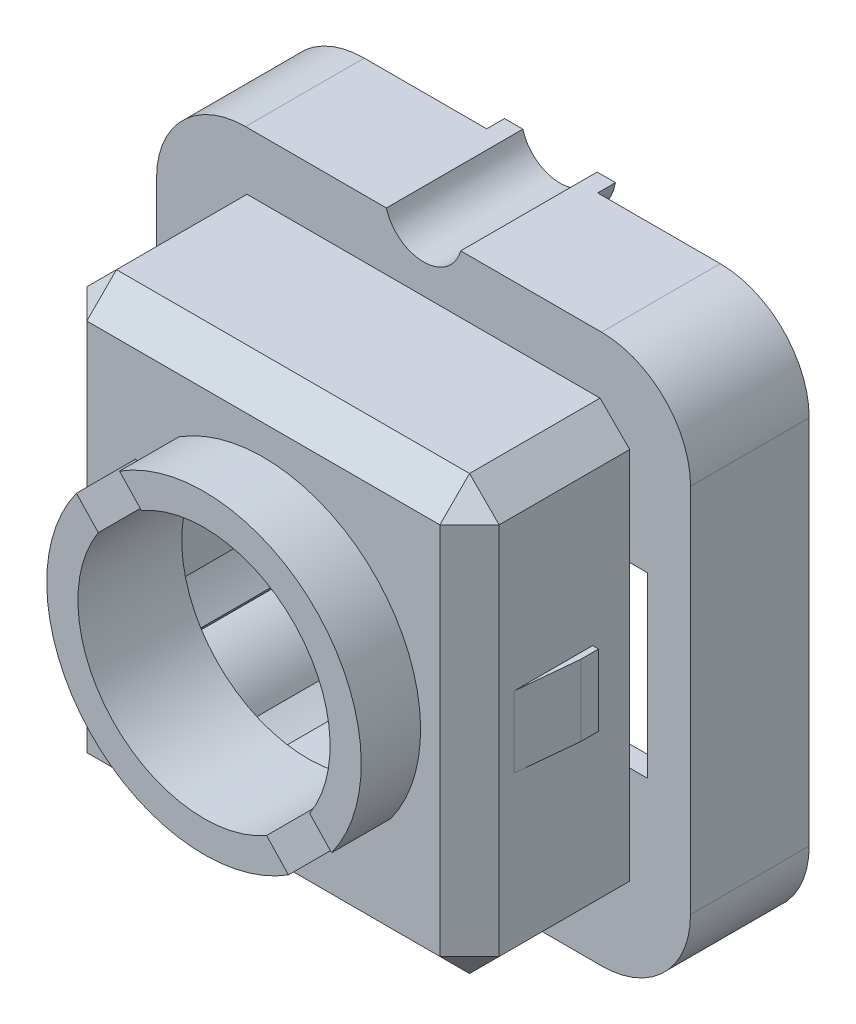
SolidWorks part; units mm, degrees
ref_plane "Plan de face" through (0, 0, 0) normal (0, 0, 1) x (1, 0, 0)
ref_plane "Plan de dessus" through (0, 0, 0) normal (0, 1, 0) x (1, 0, 0)
ref_plane "Plan de droite" through (0, 0, 0) normal (1, 0, 0) x (0, 0, -1)
sketch "Sketch1" plane through (0, 0, 0) normal (0, 0, 1) x (1, 0, 0)
  line L0 (-3, -8.25) -> (-3, -3.25)
  line L1 (-9, 9.25) -> (9, 9.25)
  line L2 (-9, 9.25) -> (-9, -9.25)
  line L3 (-9, -9.25) -> (9, -9.25)
  line L4 (9, 9.25) -> (9, -9.25)
  line L5 (-8.2, 8.25) -> (3, 8.25)
  line L6 (-8.2, 8.25) -> (-8.2, -3.25)
  line L7 (-3, -8.25) -> (8.2, -8.25)
  line L8 (8.2, 3.25) -> (8.2, -8.25)
  line L10 (3, 8.25) -> (3, 3.25)
  line L11 (3, 3.25) -> (7.4738, 3.25)
  line L15 (-8.2, -3.25) -> (-3, -3.25)
  line L17 (7.4738, 3.25) -> (8.2, 3.25)
  line L18 (0, 0) -> (0, 17.8809) construction
  line L19 (0, 0) -> (0, -19.0945) construction
  dimension "D1" = 18
  dimension "D2" = 18.5
  dimension "D3" = 1
  dimension "D4" = 0.8
  dimension "D5" = 0.8
  dimension "D6" = 1
  dimension "D7" = 6
  dimension "D8" = 6
  dimension "D9" = 6
  dimension "D10" = 6
  dimension "D11" = 9
  dimension "D12" = 9.25
extrude "Boss-Extrude1" add sketch "Sketch1" along normal blind 3.3
sketch "Sketch2" plane through (0, 0, 3.3) normal (0, 0, 1) x (1, 0, 0)
  line L0 (-6, 6.5) -> (3, 6.5)
  line L1 (-9, 9.25) -> (9, 9.25)
  line L2 (-9, 9.25) -> (-9, -9.25)
  line L3 (-9, -9.25) -> (9, -9.25)
  line L4 (9, 9.25) -> (9, -9.25)
  line L5 (3, 3.25) -> (3, 8.25) construction
  line L6 (3, 6.5) -> (3, 3.25)
  line L7 (3, 3.25) -> (6, 3.25)
  line L8 (8.2, 3.25) -> (3, 3.25) construction
  line L9 (6, 3.25) -> (6, -6.5)
  line L10 (6, -6.5) -> (-3, -6.5)
  line L11 (-3, -3.25) -> (-3, -8.25) construction
  line L12 (-3, -6.5) -> (-3, -3.25)
  line L13 (-3, -3.25) -> (-6, -3.25)
  line L14 (-8.2, -3.25) -> (-3, -3.25) construction
  line L15 (-6, -3.25) -> (-6, 6.5)
  dimension "D1" = 12
  dimension "D2" = 6
  dimension "D3" = 13
  dimension "D4" = 6.5
extrude "Boss-Extrude2" add sketch "Sketch2" along normal blind 0.7
fillet "Fillet1" radius 3 4 edges at (-9, -9.25, 2) (9, -9.25, 2) (-9, 9.25, 2) (9, 9.25, 2)
sketch "Sketch3" plane through (0, 0, 4) normal (0, 0, 1) x (1, 0, 0)
  line L0 (-6, 6.5) -> (3, 6.5)
  line L1 (-6.95, 7.3) -> (6.95, 7.3)
  line L2 (-6.95, 7.3) -> (-6.95, -7.3)
  line L3 (-6.95, -7.3) -> (6.95, -7.3)
  line L4 (6.95, 7.3) -> (6.95, -7.3)
  line L5 (3, 6.5) -> (3, 3.25)
  line L6 (3, 3.25) -> (6, 3.25)
  line L7 (6, 3.25) -> (6, -6.5)
  line L8 (6, -6.5) -> (-3, -6.5)
  line L9 (-3, -3.25) -> (-3, -6.5) construction
  line L10 (-3, -6.5) -> (6, -6.5) construction
  line L11 (-3, -6.5) -> (-3, -3.25)
  line L12 (-6, -3.25) -> (-3, -3.25) construction
  line L13 (-3, -3.25) -> (-6, -3.25)
  line L14 (-6, -3.25) -> (-6, 6.5)
  dimension "D1" = 13.9
  dimension "D2" = 14.6
  dimension "D3" = 7.3
  dimension "D4" = 6.95
extrude "Boss-Extrude3" add sketch "Sketch3" along normal blind 3.9
sketch "Sketch4" plane through (0, 0, 7.9) normal (0, 0, 1) x (1, 0, 0)
  line L0 (-6.95, -7.3) -> (6.95, -7.3) construction
  line L1 (-6.95, 7.3) -> (6.95, 7.3)
  line L2 (-6.95, 7.3) -> (-6.95, -7.3)
  line L3 (-6.95, -7.3) -> (6.95, -7.3)
  line L4 (6.95, 7.3) -> (6.95, -7.3)
  line L5 (-6.95, -7.3) -> (6.95, -7.3) construction
  circle A0 centre (0, 0) radius 4.25
  dimension "D1" = 8.5
extrude "Boss-Extrude4" add sketch "Sketch4" along normal blind 1.5
chamfer "Chamfer1" distance 1 angle 45 8 edges at (-6.95, 0, 9.4) (-6.95, -7.3, 6.7) (0, -7.3, 9.4) (6.95, -7.3, 6.7) (6.95, 0, 9.4) (-6.95, 7.3, 6.7) (0, 7.3, 9.4) (6.95, 7.3, 6.7)
sketch "Sketch5" plane through (0, 0, 9.4) normal (0, 0, 1) x (1, 0, 0)
  line L0 (-5.95, 6.3) -> (5.95, -6.3) construction
  line L1 (-2.8467, 4.4706) -> (-2.1092, 3.6897)
  line L3 (2.8467, -4.4706) -> (2.1092, -3.6897)
  line L5 (-3.5632, 2.3164) -> (-4.3008, 3.0973)
  line L6 (3.5632, -2.3164) -> (4.3008, -3.0973)
  arc A0 (3.5632, -2.3164) -> (-2.1092, 3.6897) centre (0, 0) ccw
  arc A1 (4.3008, -3.0973) -> (-2.8467, 4.4706) centre (0, 0) ccw
  arc A2 (-3.5632, 2.3164) -> (2.1092, -3.6897) centre (0, 0) ccw
  arc A3 (-4.3008, 3.0973) -> (2.8467, -4.4706) centre (0, 0) ccw
  dimension "D1" = 10.6
  dimension "D2" = 2
  dimension "D3" = 1
extrude "Boss-Extrude5" add sketch "Sketch5" along normal blind 2
sketch "Sketch6" plane through (0, 0, 4) normal (0, 0, 1) x (1, 0, 0)
  line L0 (6.95, -6.3) -> (6.95, 6.3) construction
  line L1 (6.95, 3) -> (7.55, 3)
  line L2 (6.95, 3) -> (6.95, -3)
  line L3 (6.95, -3) -> (7.55, -3)
  line L4 (7.55, 3) -> (7.55, -3)
  line L5 (6.95, 3) -> (-11.0995, 3) construction
  line L6 (6.95, -3) -> (-12.7288, -3) construction
  line L7 (-6.95, -6.3) -> (-6.95, 6.3) construction
  line L8 (-6.95, 3) -> (-7.55, 3)
  line L9 (-6.95, 3) -> (-6.95, -3)
  line L10 (-6.95, -3) -> (-7.55, -3)
  line L11 (-7.55, 3) -> (-7.55, -3)
  dimension "D1" = 6
  dimension "D2" = 3
  dimension "D3" = 0.6
  dimension "D4" = 0.6
extrude "Cut-Extrude1" cut sketch "Sketch6" against normal through all
sketch "Sketch7" plane through (6.95, 0, 0) normal (1, 0, 0) x (0, 0, -1)
  line L0 (-4, 3) -> (-7.0212, 3) construction
  line L1 (-0.848, -3) -> (-5.2554, -3) construction
  line L2 (-3.3, 3) -> (-1.1129, 3) construction
  line L3 (-4, -6.25) -> (-4, 6.25) construction
  line L4 (-4, 3) -> (-3.3, 3)
  line L5 (-4, 3) -> (-4, -3)
  line L6 (-4, -3) -> (-3.3, -3)
  line L7 (-3.3, 3) -> (-3.3, -3)
  line L8 (-3.3, -8.25) -> (-3.3, 3.25) construction
  dimension "D1" = 0
  dimension "D2" = 0
extrude "Cut-Extrude2" cut sketch "Sketch7" against normal blind 14
sketch "Sketch8" plane through (6.95, 0, 0) normal (1, 0, 0) x (0, 0, -1)
  line L0 (-8.4, 6.3) -> (-8.4, -6.3) construction
  line L1 (-7.9, 1.2) -> (-5.25, 1.2)
  line L2 (-7.9, 1.2) -> (-7.9, -1.2)
  line L3 (-7.9, -1.2) -> (-5.25, -1.2)
  line L4 (-5.25, 1.2) -> (-5.25, -1.2)
  line L5 (-4, -6.25) -> (-4, 6.25) construction
  dimension "D1" = 2.4
  dimension "D2" = 1.2
  dimension "D3" = 0.5
  dimension "D4" = 1.25
extrude "Boss-Extrude6" add sketch "Sketch8" along normal blind 0.2
sketch "Sketch9" plane through (-6.95, 0, 0) normal (-1, 0, 0) x (0, 0, 1)
  line L0 (8.4, -6.3) -> (8.4, 6.3) construction
  line L1 (5.25, 1.2) -> (7.9, 1.2)
  line L2 (5.25, 1.2) -> (5.25, -1.2)
  line L3 (5.25, -1.2) -> (7.9, -1.2)
  line L4 (7.9, 1.2) -> (7.9, -1.2)
  line L5 (4, 6.25) -> (4, -6.25) construction
  dimension "D1" = 2.4
  dimension "D2" = 1.2
  dimension "D3" = 0.5
  dimension "D4" = 1.25
extrude "Boss-Extrude7" add sketch "Sketch9" along normal blind 0.2
sketch "Sketch10" plane through (0, -1.2, 0) normal (0, -1, 0) x (1, 0, 0)
  line L0 (-6.95, 7.9) -> (-7.15, 5.85)
  line L1 (-7.15, 5.25) -> (-7.15, 7.9) construction
  line L2 (-7.15, 5.85) -> (-7.15, 7.9)
  line L3 (-7.15, 7.9) -> (-6.95, 7.9)
  line L4 (6.95, 7.9) -> (7.15, 5.85)
  line L5 (7.15, 7.9) -> (7.15, 5.25) construction
  line L6 (7.15, 5.85) -> (7.15, 7.9)
  line L7 (7.15, 7.9) -> (6.95, 7.9)
  dimension "D1" = 0.6
  dimension "D2" = 0.6
extrude "Cut-Extrude3" cut sketch "Sketch10" against normal through all
sketch "Sketch11" plane through (0, 0, 0) normal (0, 0, -1) x (-1, 0, 0)
  line L0 (0, 0) -> (-3, 3.25) construction
  line L1 (-3, 3.25) -> (-5.2906, 5.7315) construction
  line L2 (0, 0) -> (8.864, -9.6026) construction
  line L3 (-4.5784, 6.8028) -> (-3.8626, 6.0274)
  line L5 (4.5784, -6.8028) -> (3.8626, -6.0274)
  line L7 (-5.6997, 4.3317) -> (-6.4154, 5.1071)
  line L8 (5.6997, -4.3317) -> (6.4154, -5.1071)
  line L9 (-5.5619, 6.0254) -> (-8.7124, 9.4384) construction
  line L10 (-6.3787, 3.25) -> (-3, 3.25)
  line L11 (-8.2, 3.25) -> (-3, 3.25) construction
  line L12 (-3, 3.25) -> (-3, 6.5)
  line L13 (3, -6.5) -> (3, -3.25)
  line L14 (3, -3.25) -> (3, -8.25) construction
  line L15 (3, -3.25) -> (6.3787, -3.25)
  line L16 (8.2, -3.25) -> (6, -3.25) construction
  arc A0 (5.6997, -4.3317) -> (6.3787, -3.25) centre (0, 0) ccw
  arc A3 (-4.5784, 6.8028) -> (-6.4154, 5.1071) centre (-7.1359, 7.7306) cw
  arc A4 (4.5784, -6.8028) -> (6.4154, -5.1071) centre (7.1359, -7.7306) cw
  arc A5 (-5.6997, 4.3317) -> (-6.3787, 3.25) centre (0, 0) ccw
  arc A6 (3, -6.5) -> (3.8626, -6.0274) centre (0, 0) ccw
  arc A7 (-3, 6.5) -> (-3.8626, 6.0274) centre (0, 0) ccw
  dimension "D1" = 2.5
  dimension "D2" = 1.25
extrude "Cut-Extrude5" cut sketch "Sketch11" against normal up to surface (7.9 mm away)
sketch "Sketch12" plane through (0, 0, 3.3) normal (0, 0, -1) x (-1, 0, 0)
  line L0 (-6, -3) -> (-7.55, -3) construction
  line L1 (-6, 3.25) -> (-6.3787, 3.25)
  line L2 (-6, 3.25) -> (-6, -3)
  line L3 (-6, -3) -> (-6.3787, -3)
  line L4 (-6.3787, 3.25) -> (-6.3787, -3)
  line L5 (6.3787, -3.25) -> (6, -3.25) construction
  line L6 (6, 3) -> (6.3787, 3)
  line L7 (6, 3) -> (6, -3.25)
  line L8 (6, -3.25) -> (6.3787, -3.25)
  line L9 (6.3787, 3) -> (6.3787, -3.25)
  line L10 (6, -3.25) -> (6.3787, -3.25) construction
  dimension "D1" = 0.3787
  dimension "D2" = 0.3787
extrude "Cut-Extrude7" cut sketch "Sketch12" against normal up to surface (4.6 mm away)
sketch "Sketch13" plane through (0, 0, 0) normal (0, 0, -1) x (-1, 0, 0)
  line L0 (0, 10.6589) -> (0, -10.2242) construction
  line L1 (-6, 9.25) -> (6, 9.25) construction
  line L2 (-1.4363, 8.25) -> (1.9748, 8.25) construction
  line L3 (-1.3, 9.8108) -> (-1.3, 7.4382) construction
  line L4 (1.3, 9.9552) -> (1.3, 7.5963) construction
  line L7 (-0.9748, -9.6) -> (1.3, -9.6) construction
  line L8 (-1.8684, 9.25) -> (-1.8684, -10.7777) construction
  line L9 (1.8684, 9.25) -> (1.8684, -11.1568) construction
  line L10 (-1.342, -7.1447) -> (-1.342, -9.25) construction
  line L12 (1.342, 8.25) -> (1.342, -7.2854) construction
  line L13 (-1.342, 8.25) -> (-1.342, -7.1447) construction
  line L14 (6, -9.25) -> (-6, -9.25) construction
  line L15 (1.342, -7.2854) -> (1.342, -11.8348) construction
  line L16 (3, -8.25) -> (-8.2, -8.25) construction
  line L17 (-1.342, -8.25) -> (1.342, -8.25)
  line L18 (-1.342, 8.25) -> (1.342, 8.25)
  arc A2 (-1.342, 8.25) -> (1.342, 8.25) centre (0, 9.595) ccw
  arc A3 (-1.342, -8.25) -> (1.342, -8.25) centre (0, -9.6) cw
  dimension "D1" = 3.8
  dimension "D2" = 1
  dimension "D3" = 9.595
  dimension "D4" = 9.6
extrude "Boss-Extrude10" add sketch "Sketch13" along direction (0, 0, -1) on the side against the normal up to next (3.3 mm away)
fillet "Fillet2" radius 2 2 edges at (-8.2, 8.25, 1.65) (8.2, -8.25, 1.65)
sketch "Sketch14" plane through (0, 0, 0) normal (0, 0, -1) x (-1, 0, 0)
  line L0 (0, -10.3387) -> (0, 13.3546) construction
  line L1 (-1.6386, 9.6) -> (3.3243, 9.6) construction
  line L2 (-1.1724, -9.6) -> (1.3996, -9.6) construction
  line L3 (-1.8711, -9.25) -> (1.8711, -9.25)
  line L4 (6, -9.25) -> (-6, -9.25) construction
  line L5 (-1.8711, 9.25) -> (1.8711, 9.25)
  line L6 (-6, 9.25) -> (6, 9.25) construction
  arc A0 (-1.8711, 9.25) -> (1.8711, 9.25) centre (0, 9.6) ccw
  arc A1 (1.8711, -9.25) -> (-1.8711, -9.25) centre (0, -9.6) ccw
  dimension "D1" = 9.6
  dimension "D2" = 9.6
extrude "Boss-Extrude11" add sketch "Sketch14" along normal blind 0.6
sketch "Sketch15" plane through (0, 0, -0.6) normal (0, 0, -1) x (-1, 0, 0)
  line L0 (0, -10.4585) -> (0, 12.9996) construction
  line L1 (-2.06, 9.6) -> (1.4654, 9.6) construction
  line L2 (-0.5883, -9.6) -> (0.815, -9.6) construction
  circle A0 centre (0, 9.6) radius 1.3
  circle A1 centre (0, -9.6) radius 1.3
  dimension "D3" = 2.6
  dimension "D4" = 2.6
  dimension "D1" = 9.6
  dimension "D2" = 9.6
extrude "Cut-Extrude8" cut sketch "Sketch15" against normal through all
